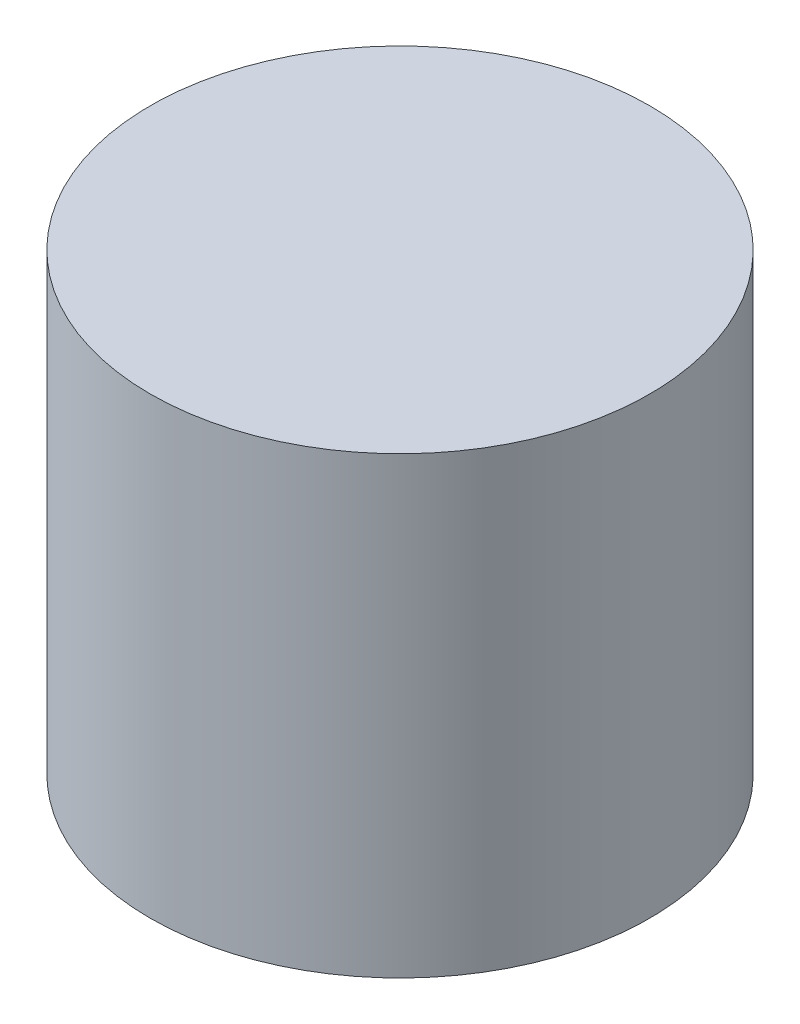
SolidWorks part; units mm, degrees
ref_plane "Front Plane" through (0, 0, 0) normal (0, 0, 1) x (1, 0, 0)
ref_plane "Top Plane" through (0, 0, 0) normal (0, 1, 0) x (1, 0, 0)
ref_plane "Right Plane" through (0, 0, 0) normal (1, 0, 0) x (0, 0, -1)
sketch "Sketch1" plane through (0, 0, 0) normal (0, 1, 0) x (1, 0, 0)
  circle A0 centre (0, 0) radius 69.85
  dimension "D1" = 139.7
extrude "Boss-Extrude1" add sketch "Sketch1" along normal blind 127
